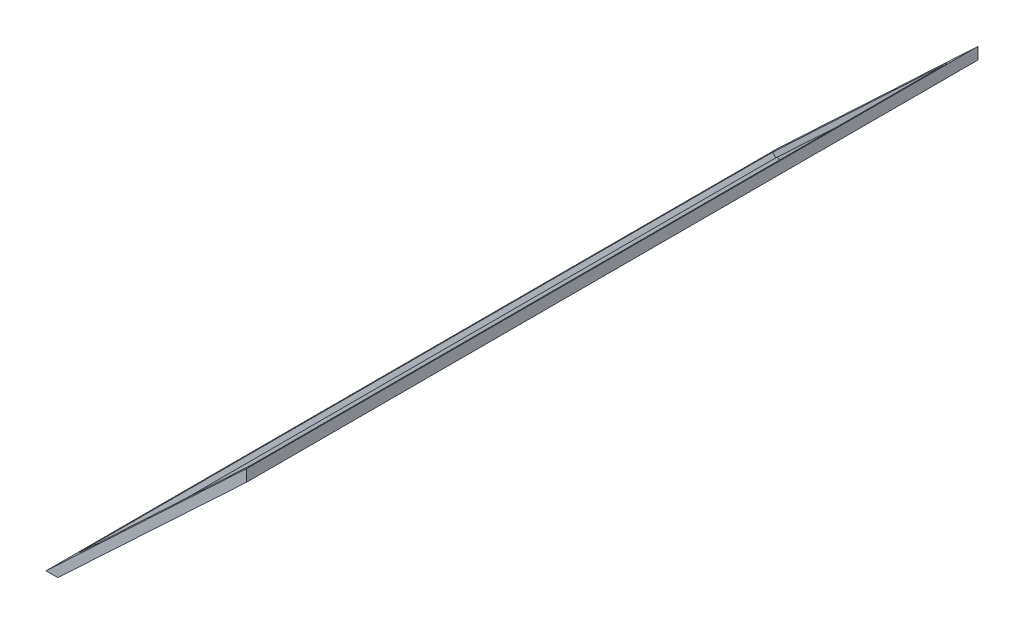
SolidWorks part; units mm, degrees
ref_plane "Alzado" through (0, 0, 0) normal (0, 0, 1) x (1, 0, 0)
ref_plane "Planta" through (0, 0, 0) normal (0, 1, 0) x (1, 0, 0)
ref_plane "Vista lateral" through (0, 0, 0) normal (1, 0, 0) x (0, 0, -1)
sketch "Croquis1" plane through (0, 0, 0) normal (0, 0, 1) x (1, 0, 0)
  line L1 (160, 0) -> (160, 150) construction
  line L2 (0, 0) -> (160, 150)
  line L7 (160, 150) -> (160, 160)
  line L8 (0, 0) -> (-10, 0)
  line L9 (-10, 0) -> (160, 160)
  dimension "D1" = 160
  dimension "D2" = 150
  dimension "D3" = 10
  dimension "D4" = 10
extrude "Saliente-Extruir1" add sketch "Croquis1" along normal blind 620
sketch "Croquis2" plane through (-4.6972, 4.9908, 0) normal (-0.6854, 0.7282, 0) x (0.7282, 0.6854, 0)
  line L0 (226.1704, -620) -> (-7.282, -620) construction
  line L1 (-7.282, -620) -> (-7.282, 0) construction
  line L2 (226.1704, -620) -> (226.1704, 0) construction
  line L3 (226.1704, 0) -> (-7.282, 0) construction
  line L4 (226.1704, -620) -> (-7.282, -620) construction
  line L5 (-7.282, -620) -> (-7.282, 0) construction
  line L6 (226.1704, -620) -> (226.1704, 0) construction
  line L7 (226.1704, 0) -> (-7.282, 0) construction
  line L8 (211.1704, -605) -> (7.718, -605)
  line L9 (7.718, -605) -> (7.718, -15)
  line L10 (211.1704, -15) -> (7.718, -15)
  line L11 (211.1704, -605) -> (211.1704, -15)
  dimension "D1" = 15
extrude "Cortar-Extruir1" cut sketch "Croquis2" against normal through all
sketch "Croquis3" plane through (0, 0, 0) normal (0.6839, -0.7295, 0) x (0.7295, 0.6839, 0)
  line L0 (226.1565, 620) -> (-7.2954, 620) construction
  line L1 (226.1565, 620) -> (226.1565, 0) construction
  line L2 (-7.2954, 620) -> (-7.2954, 0) construction
  line L3 (226.1565, 0) -> (-7.2954, 0) construction
  line L4 (226.1565, 620) -> (-7.2954, 620) construction
  line L5 (226.1565, 620) -> (226.1565, 0) construction
  line L6 (-7.2954, 620) -> (-7.2954, 0) construction
  line L7 (226.1565, 0) -> (-7.2954, 0) construction
  line L8 (216.1565, 610) -> (2.7046, 610)
  line L9 (2.7046, 610) -> (2.7046, 10)
  line L10 (216.1565, 10) -> (2.7046, 10)
  line L11 (216.1565, 610) -> (216.1565, 10)
  dimension "D1" = 10
extrude "Cortar-Extruir2" cut sketch "Croquis3" against normal blind 3
